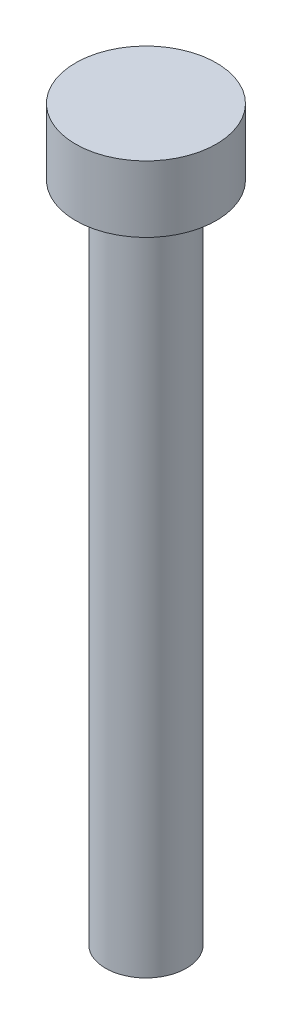
SolidWorks part; units mm, degrees
ref_plane "Front Plane" through (0, 0, 0) normal (0, 0, 1) x (1, 0, 0)
ref_plane "Top Plane" through (0, 0, 0) normal (0, 1, 0) x (1, 0, 0)
ref_plane "Right Plane" through (0, 0, 0) normal (1, 0, 0) x (0, 0, -1)
sketch "Sketch1" plane through (0, 0, 0) normal (0, 1, 0) x (1, 0, 0)
  circle A0 centre (0, 0) radius 4.25
  dimension "D1" = 8.5
extrude "Boss-Extrude1" add sketch "Sketch1" along normal blind 4
sketch "Sketch2" plane through (0, 0, 0) normal (0, -1, 0) x (1, 0, 0)
  circle A0 centre (0, 0) radius 2.44
  dimension "D1" = 4.88
extrude "Boss-Extrude2" add sketch "Sketch2" along normal blind 40
